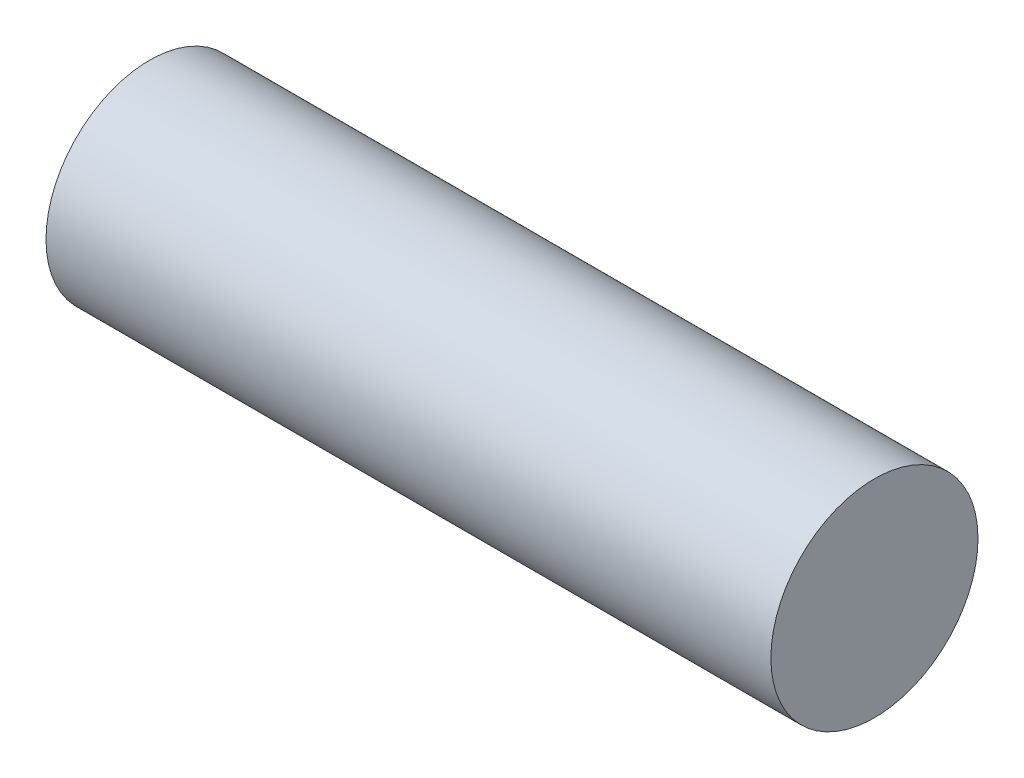
SolidWorks part; units mm, degrees
ref_plane "Front Plane" through (0, 0, 0) normal (0, 0, 1) x (1, 0, 0)
ref_plane "Top Plane" through (0, 0, 0) normal (0, 1, 0) x (1, 0, 0)
ref_plane "Right Plane" through (0, 0, 0) normal (1, 0, 0) x (0, 0, -1)
sketch "Sketch1" plane through (0, 0, 0) normal (1, 0, 0) x (0, 0, -1)
  circle A0 centre (0, 0) radius 6.35
  dimension "D1" = 12.7
extrude "Boss-Extrude1" add sketch "Sketch1" along normal mid plane 44.45
